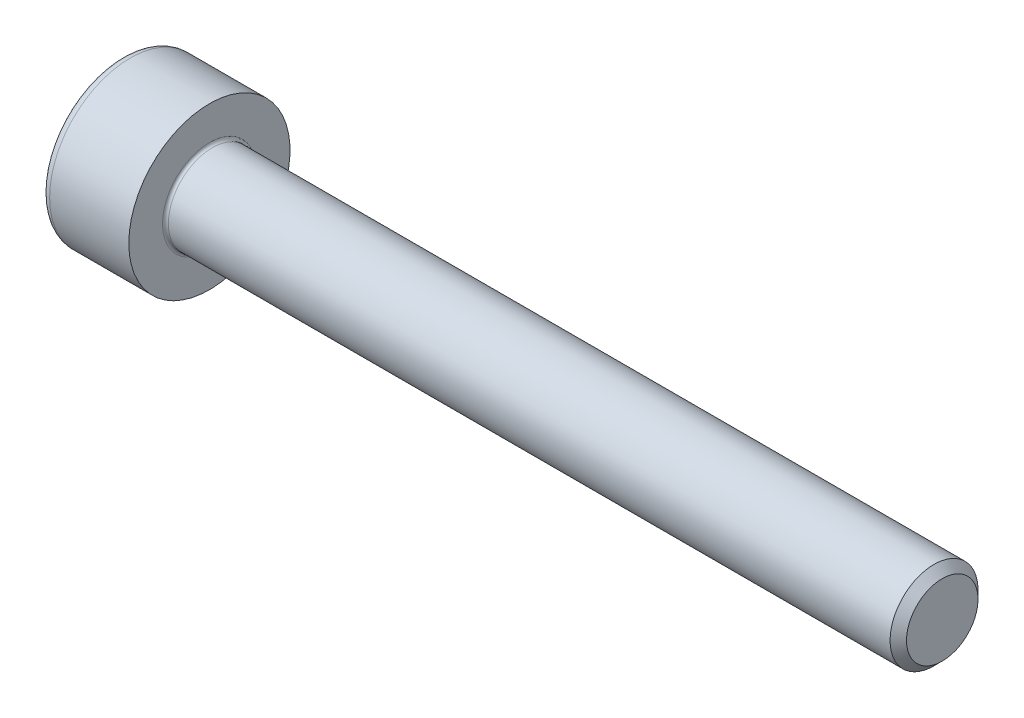
SolidWorks part; units mm, degrees
ref_plane "Plane1" through (0, 0, 0) normal (0, 0, 1) x (1, 0, 0)
ref_plane "Plane2" through (0, 0, 0) normal (0, 1, 0) x (1, 0, 0)
ref_plane "Plane3" through (0, 0, 0) normal (1, 0, 0) x (0, 0, -1)
sketch "BodySke" plane through (0, 0, 0) normal (0, 0, 1) x (1, 0, 0)
  line L0 (0, 0) -> (0, 2.75)
  line L1 (0, 2.75) -> (3, 2.75)
  line L2 (3, 2.75) -> (3, 1.5)
  line L3 (3, 1.5) -> (27.7195, 1.5)
  line L4 (28, 1.2195) -> (28, 0)
  line L5 (28, 0) -> (0, 0)
  line L6 (-31.75, 0) -> (127, 0) construction
  line L8 (28, 1.2195) -> (27.7195, 1.5)
  line L10 (28, -1.2195) -> (27.7195, -1.5) construction
  line L11 (3.5, 9.525) -> (3.5, 3.175) construction
  line L12 (3, 9.525) -> (3, 3.175) construction
  line L13 (-32, 9.525) -> (-32, 3.175) construction
  dimension "Diameter" = 3
  dimension "Head_ht" = 3
  dimension "Length" = 25
  dimension "Body_ch_ang" = 45
  dimension "Head_dia" = 5.5
  dimension "Minor_dia" = 2.439
  dimension "Advance" = 0.5
  dimension "Thread_nom" = 25
  dimension "Thread_length" = 60
revolve "Base-Revolve" add sketch "BodySke"
cosmetic thread "ThreadCosmetic"
fillet "Fillet1" radius 0.1 1 edges at (3, 0, 1.5)
fillet "Fillet2" radius 0.3 1 edges at (0, 0, 2.75)
sketch "Sketch2" plane through (0, 0, 0) normal (0, 0, 1) x (1, 0, 0)
  line L0 (0, 1.26) -> (1.3, 1.26)
  line L1 (1.3, 1.26) -> (2.0275, 0)
  line L2 (-31.75, 0) -> (127, 0) construction
  line L3 (2.0275, 0) -> (0, 0)
  line L4 (0, 0) -> (0, 1.26)
  line L6 (0, 0) -> (47.625, 0) construction
  dimension "D1" = 1.26
  dimension "D2" = 60
  dimension "Depth" = 1.3
revolve "Hex-PreBroach" cut sketch "Sketch2" angle 360 about L6
sketch "Sketch3" plane through (0, 0, 0) normal (-1, 0, 0) x (0, 0.5, 0.866)
  line L0 (0.7275, 1.26) -> (-0.7275, 1.26)
  line L1 (-0.7275, 1.26) -> (-1.4549, 0)
  line L2 (0.7275, 1.26) -> (1.4549, 0)
  line L3 (0.7275, -1.26) -> (1.4549, 0)
  line L4 (0.7275, -1.26) -> (-0.7275, -1.26)
  line L5 (-0.7275, -1.26) -> (-1.4549, 0)
  dimension "D1" = 1.26
  dimension "D2" = 1.26
  dimension "Hex_size" = 2.52
extrude "Hex" cut sketch "Sketch3" against normal blind 1.3
sketch "ThdSchSke" plane through (0, 0, 0) normal (0, 0, 1) x (1, 0, 0)
  line L0 (4.5, -1.2195) -> (4.3036, -1.5)
  line L1 (4.5, -1.2195) -> (4.6964, -1.5)
  line L2 (4.6964, -1.5) -> (4.6964, -1.875)
  line L3 (-3.175, 0) -> (5.1513, 0) construction
  line L4 (0, 2.45) -> (0, -2.45) construction
  line L5 (4.6964, -1.875) -> (4.3036, -1.875)
  line L6 (4.3036, -1.875) -> (4.3036, -1.5)
  dimension "Thread_minor" = 2.439
  dimension "Diameter" = 3
  dimension "Start" = 4.5
  dimension "SideAngle" = 55
  dimension "VeeAngle" = 70
  dimension "Overcut" = 3.75
revolve "ThreadSchematic" [suppressed] cut sketch "ThdSchSke" angle 360 about L3
pattern_linear "ThdSchPat" [suppressed]
equation "\"D2@Sketch3\" = \"Hex_size@Sketch3\" / 2"
equation "\"D1@Sketch3\" = \"Hex_size@Sketch3\" / 2"
equation "\"D1@Sketch2\" = \"Hex_size@Sketch3\" / 2"
equation "\"Thread_minor@ThreadCosmetic\"  =  \"Minor_dia@BodySke\""
equation "\"Depth@Sketch2\" =  \"Key_eng@Hex\""
equation "\"Thread_length@ThreadCosmetic\" = ((sgn( (\"Length@BodySke\" - \"Advance@BodySke\" * 3.0) - \"Thread_nom@BodySke\" )-1)*( (\"Length@BodySke\" - \"Advance@BodySke\" * 3.0) - \"Thread_nom@BodySke\" ))/-2+ \"Thread_nom@BodySke\""
equation "\"Thread_minor@ThdSchSke\" = \"Minor_dia@BodySke\""
equation "\"Diameter@ThdSchSke\" = \"Diameter@BodySke\""
equation "\"Overcut@ThdSchSke\" = \"Diameter@BodySke\" * 1.25"
equation "\"Start@ThdSchSke\" = \"Head_ht@BodySke\" + \"Length@BodySke\" - \"Thread_length@ThreadCosmetic\"  '---Non-countersunk---"
equation "\"Num_threads@ThdSchPat\" = int( \"Thread_length@ThreadCosmetic\" / \"Advance@BodySke\" + 0.999 )  + 1"
equation "\"Advance@ThdSchPat\" = \"Thread_length@ThreadCosmetic\" /  (\"Num_threads@ThdSchPat\" - 1) 'relax it"
equation "\"Num_threads@ThdSchPat\" = \"Num_threads@ThdSchPat\" - sgn( \"Num_threads@ThdSchPat\" - 1) '---chamfered tips only---"
